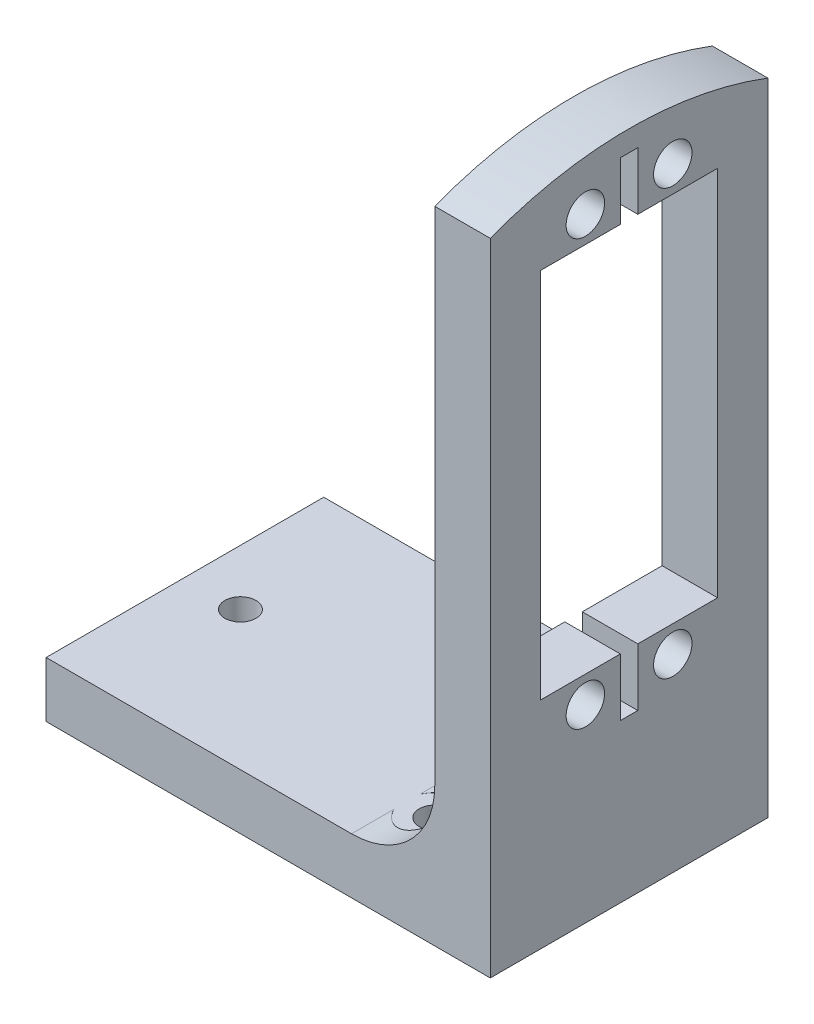
SolidWorks part; units mm, degrees
ref_plane "Front Plane" through (0, 0, 0) normal (0, 0, 1) x (1, 0, 0)
ref_plane "Top Plane" through (0, 0, 0) normal (0, 1, 0) x (1, 0, 0)
ref_plane "Right Plane" through (0, 0, 0) normal (1, 0, 0) x (0, 0, -1)
sketch "Sketch3" plane through (0, 0, 0) normal (1, 0, 0) x (0, 0, -1)
  line L0 (5.748, 60.8575) -> (26.002, 18.3125) construction
  line L1 (0, 0) -> (31.75, 0)
  line L2 (0, 0) -> (0, 73.5575)
  line L3 (0, 73.5575) -> (31.75, 73.5575)
  line L4 (31.75, 0) -> (31.75, 73.5575)
  line L5 (5.748, 60.8575) -> (14.875, 60.8575)
  line L6 (5.748, 60.8575) -> (5.748, 18.3125)
  line L7 (5.748, 18.3125) -> (14.875, 18.3125)
  line L8 (26.002, 60.8575) -> (26.002, 18.3125)
  line L9 (26.002, 60.8575) -> (5.748, 18.3125) construction
  line L10 (10.875, 63.885) -> (20.875, 15.285) construction
  line L11 (10.875, 15.285) -> (20.875, 63.885) construction
  line L12 (16.875, 18.3125) -> (26.002, 18.3125)
  line L13 (14.875, 18.3125) -> (14.875, 11.7085)
  line L14 (14.875, 11.7085) -> (16.875, 11.7085)
  line L15 (16.875, 18.3125) -> (16.875, 11.7085)
  line L16 (15.875, 39.585) -> (-939.9401, 39.585) construction
  line L17 (14.875, 67.4615) -> (16.875, 67.4615)
  line L18 (14.875, 60.8575) -> (14.875, 67.4615)
  line L19 (16.875, 60.8575) -> (16.875, 67.4615)
  line L20 (16.875, 60.8575) -> (26.002, 60.8575)
  circle A0 centre (10.875, 15.285) radius 2.2
  circle A1 centre (20.875, 15.285) radius 2.2
  circle A2 centre (10.875, 63.885) radius 2.2
  circle A3 centre (20.875, 63.885) radius 2.2
  point P13 (15.875, 11.7085)
  point P22 (15.875, 39.585)
  point P23 (15.875, 39.585)
  point P32 (15.875, 29.9575)
  point P33 (15.875, 49.2125)
  point P34 (15.875, 0)
  dimension "D3" = 4.4
  dimension "D1" = 10
  dimension "D2" = 48.6
  dimension "D4" = 42.545
  dimension "D5" = 20.254
  dimension "D6" = 2
  dimension "D7" = 6.604
  dimension "D12" = 12.7
  dimension "D10" = 31.75
  dimension "D8" = 30.9
  dimension "D9" = 49.2125
extrude "Boss-Extrude1" add sketch "Sketch3" along normal blind 6.35
sketch "Sketch5" plane through (6.35, 0, 0) normal (1, 0, 0) x (0, 0, -1)
  line L1 (0, 0) -> (31.75, 0)
  line L2 (0, 0) -> (0, -6.35)
  line L3 (0, -6.35) -> (31.75, -6.35)
  line L4 (31.75, 0) -> (31.75, -6.35)
  dimension "D1" = 6.35
extrude "Boss-Extrude2" add sketch "Sketch5" against normal blind 50.8
fillet "Fillet1" radius 9.525 1 edges at (0, 0, -15.875)
sketch "Sketch6" plane through (0, 0, 0) normal (0, 1, 0) x (1, 0, 0)
  line L0 (-44.45, 0) -> (-9.525, 0) construction
  line L2 (-44.45, 31.75) -> (-44.45, 0) construction
  line L3 (0, 15.875) -> (-33.0413, 15.875) construction
  line L5 (0, 31.75) -> (0, 0) construction
  circle A0 centre (-6.35, 6.35) radius 1.777
  circle A2 centre (-38.1, 15.875) radius 1.777
  circle A3 centre (-6.35, 25.4) radius 1.777
  dimension "D1" = 3.554
  dimension "D2" = 6.35
  dimension "D4" = 6.35
  dimension "D3" = 6.35
extrude "Cut-Extrude1" cut sketch "Sketch6" against normal through all both and the other way through all
sketch "Sketch7" plane through (6.35, 0, 0) normal (1, 0, 0) x (0, 0, -1)
  line L0 (31.75, 73.5575) -> (0, 73.5575) construction
  line L1 (0, -6.35) -> (31.75, -6.35) construction
  line L2 (0, 66.9185) -> (0, 82.7489)
  line L3 (0, 73.5575) -> (0, -6.35) construction
  line L4 (0, 82.7489) -> (31.75, 82.7489)
  line L5 (31.75, 82.7489) -> (31.75, 66.9185)
  line L6 (31.75, -6.35) -> (31.75, 73.5575) construction
  arc A0 (31.75, 66.9185) -> (0, 66.9185) centre (15.875, 25.4) ccw
  point P6 (15.875, 73.5575)
  dimension "D2" = 88.9
  dimension "D1" = 31.75
extrude "Cut-Extrude2" cut sketch "Sketch7" against normal through all
sketch "Sketch8" plane through (0, 0, 0) normal (0, 1, 0) x (1, 0, 0)
  circle A0 centre (-6.35, 25.4) radius 3.5
  circle A1 centre (-6.35, 6.35) radius 3.5
  dimension "D1" = 7
extrude "Cut-Extrude3" cut sketch "Sketch8" along normal through all
equation "\"D1@Sketch6\" = 3.3mm + \"normtol\""
equation "\"tighttol\" = 0.005in"
equation "\"normtol\" = 0.01in"
equation "\"loosetol\" = 0.02in"
equation "\"Fry height\"= 0.5in"
equation "\"Fry spacing\"= 0.5625in"
equation "\"Potato width\"= \"Fry spacing\" * 4"
equation "\"Potato length\"= 80mm"
equation "\"top robot surface separation\" = 0.6875"
equation "\"D9@Sketch3\"=1.25+\"top robot surface separation\""
equation "\"D1@Sketch8\"=7mm"
